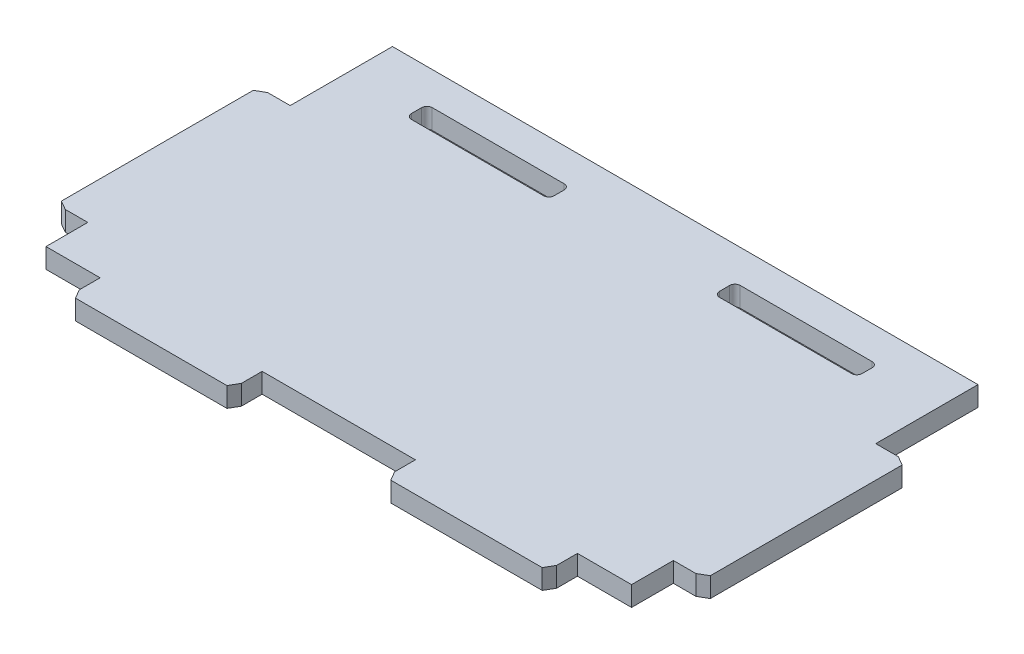
SolidWorks part; units mm, degrees
ref_plane "Front Plane" through (0, 0, 0) normal (0, 0, 1) x (1, 0, 0)
ref_plane "Top Plane" through (0, 0, 0) normal (0, 1, 0) x (1, 0, 0)
ref_plane "Right Plane" through (0, 0, 0) normal (1, 0, 0) x (0, 0, -1)
sketch "Sketch1" plane through (0, 0, 0) normal (0, 1, 0) x (1, 0, 0)
  line L1 (-46.8266, 25) -> (46.8266, 25)
  line L2 (-46.8266, 25) -> (-46.8266, -25)
  line L3 (-46.8266, -25) -> (46.8266, -25)
  line L4 (46.8266, 25) -> (46.8266, -25)
  line L5 (-46.8266, 25) -> (46.8266, -25) construction
  line L6 (-46.8266, -25) -> (46.8266, 25) construction
  point P0 (0, 0)
  dimension "D1" = 93.6531
  dimension "D2" = 50
extrude "Boss-Extrude1" add sketch "Sketch1" along normal blind 2.8575
sketch "Sketch3" plane through (0, 0, 0) normal (0, -1, 0) x (1, 0, 0)
  line L0 (-46.8266, 25) -> (46.8266, 25) construction
  line L2 (-34.1266, 25) -> (-34.1266, 29.318) construction
  line L5 (-34.1266, 29.318) -> (-11.3755, 29.318) construction
  line L6 (-11.3755, 29.318) -> (-11.3755, 25) construction
  line L7 (-11.3755, 25) -> (-34.1266, 25) construction
  line L8 (-11.3755, 27.159) -> (11.3755, 27.159) construction
  line L9 (11.3755, 29.318) -> (34.1266, 29.318) construction
  line L10 (11.3755, 29.318) -> (11.3755, 25) construction
  line L11 (11.3755, 25) -> (34.1266, 25) construction
  line L12 (34.1266, 29.318) -> (34.1266, 25) construction
  line L13 (-46.8266, -25) -> (-46.8266, 25) construction
  line L14 (34.1266, 27.159) -> (46.8266, 27.159) construction
  line L15 (46.8266, 27.159) -> (46.8266, 25) construction
  line L16 (-34.1266, 27.159) -> (-46.8266, 27.159) construction
  line L17 (-46.8266, 27.159) -> (-46.8266, 25) construction
  line L18 (-34.4441, 25) -> (-34.4441, 29.318)
  line L19 (-34.4441, 29.318) -> (-11.058, 29.318)
  line L20 (-11.058, 29.318) -> (-11.058, 25)
  line L21 (11.058, 25) -> (11.058, 29.318)
  line L22 (11.058, 29.318) -> (34.4441, 29.318)
  line L23 (34.4441, 29.318) -> (34.4441, 25)
  line L24 (-22.751, 29.318) -> (-22.751, 25) construction
  line L25 (22.751, 29.318) -> (22.751, 25) construction
  line L26 (-11.058, 25) -> (-34.4441, 25)
  line L27 (11.058, 25) -> (34.4441, 25)
  dimension "D1" = 4.318
  dimension "D2" = 12.7
  dimension "D3" = 0.3175
extrude "Boss-Extrude2" add sketch "Sketch3" against normal up to surface (2.8575 mm away) up to face at (0, 2.8575, 0)
sketch "Sketch4" plane through (0, 2.8575, 0) normal (0, 1, 0) x (1, 0, 0)
  line L6 (46.8266, 25) -> (42.2546, 25)
  line L7 (46.8266, 25) -> (46.8266, 10.2425)
  line L8 (46.8266, 10.2425) -> (42.2546, 10.2425)
  line L9 (42.2546, 25) -> (42.2546, 10.2425)
  line L10 (46.8266, -25) -> (42.2546, -25)
  line L11 (46.8266, -25) -> (46.8266, -18.9675)
  line L12 (46.8266, -18.9675) -> (42.2546, -18.9675)
  line L13 (42.2546, -25) -> (42.2546, -18.9675)
  line L14 (-46.8266, -18.65) -> (46.8266, -18.65) construction
  line L15 (46.8266, -25) -> (46.8266, 25) construction
  line L16 (-46.8266, 9.925) -> (46.8266, 9.925) construction
  line L17 (44.5406, -18.9675) -> (44.5406, -18.65) construction
  line L18 (44.5406, 10.2425) -> (44.5406, 9.925) construction
  line L19 (46.8266, 25) -> (-46.8266, 25) construction
  line L20 (-46.8266, 21.825) -> (46.8266, 21.825) construction
  line L21 (-46.8266, 21.825) -> (-46.8266, 17.253) construction
  line L22 (-46.8266, 17.253) -> (46.8266, 17.253) construction
  line L23 (46.8266, 21.825) -> (46.8266, 17.253) construction
  line L24 (-46.8266, -25) -> (-34.4441, -25) construction
  line L25 (-46.8266, 25) -> (-42.2546, 25)
  line L26 (-46.8266, 25) -> (-46.8266, 10.2425)
  line L27 (-46.8266, 10.2425) -> (-42.2546, 10.2425)
  line L28 (-42.2546, 25) -> (-42.2546, 10.2425)
  line L29 (-46.8266, -25) -> (-42.2546, -25)
  line L30 (-46.8266, -25) -> (-46.8266, -18.9675)
  line L31 (-46.8266, -18.9675) -> (-42.2546, -18.9675)
  line L32 (-42.2546, -25) -> (-42.2546, -18.9675)
  line L33 (-46.8266, 25) -> (-46.8266, -25) construction
  dimension "D1" = 28.575
  dimension "D2" = 6.35
  dimension "D3" = 0.3175
  dimension "D4" = 4.572
  dimension "D6" = 3.175
extrude "Cut-Extrude1" cut sketch "Sketch4" against normal up to next
sketch "Sketch5" plane through (0, 0, 0) normal (0, -1, 0) x (1, 0, 0)
  line L0 (0, -25) -> (0, 0) construction
  line L1 (12.7, -17.253) -> (31.75, -17.253) construction
  line L2 (12.7, -17.253) -> (12.7, -20.1105) construction
  line L3 (12.7, -20.1105) -> (31.75, -20.1105) construction
  line L4 (31.75, -17.253) -> (31.75, -20.1105) construction
  line L5 (42.2546, -25) -> (-42.2546, -25) construction
  line L6 (-31.75, -17.253) -> (-12.7, -17.253) construction
  line L7 (-46.8266, -17.253) -> (46.8266, -17.253) construction
  line L9 (11.938, -17.253) -> (32.512, -17.253)
  line L14 (32.512, -17.253) -> (32.512, -20.2375)
  line L15 (11.938, -20.2375) -> (32.512, -20.2375)
  line L16 (11.938, -17.253) -> (11.938, -20.2375)
  line L17 (-31.75, -17.253) -> (-31.75, -20.1105) construction
  line L18 (-31.75, -20.1105) -> (-12.7, -20.1105) construction
  line L19 (-12.7, -17.253) -> (-12.7, -20.1105) construction
  line L21 (-31.75, -18.6818) -> (-32.512, -18.6818) construction
  line L22 (-32.512, -17.253) -> (-11.938, -17.253)
  line L23 (-11.938, -17.253) -> (-11.938, -20.2375)
  line L24 (-32.512, -20.2375) -> (-11.938, -20.2375)
  line L25 (-32.512, -17.253) -> (-32.512, -20.2375)
  line L26 (-12.7, -18.6818) -> (-11.938, -18.6818) construction
  line L27 (12.7, -18.6818) -> (11.938, -18.6818) construction
  line L28 (31.75, -18.6818) -> (32.512, -18.6818) construction
  line L32 (-22.225, -17.253) -> (-22.225, -20.1105) construction
  line L33 (22.225, -17.253) -> (22.225, -20.1105) construction
  dimension "D1" = 2.8575
  dimension "D2" = 19.05
  dimension "D3" = 0.127
  dimension "D4" = 0.762
  dimension "D5" = 44.45
  dimension "D8" = 0.762
extrude "Cut-Extrude2" cut sketch "Sketch5" against normal up to next
sketch "Sketch6" plane through (0, 0, 0) normal (0, -1, 0) x (1, 0, 0)
  line L0 (-44.2866, 4.3625) -> (-46.8266, 4.3625) construction
  line L19 (-46.8266, -10.2425) -> (-46.8266, 18.9675) construction
  line L20 (44.2866, 4.3625) -> (46.8266, 4.3625) construction
  line L21 (46.8266, 18.9675) -> (46.8266, -10.2425) construction
  line L33 (-22.751, 26.778) -> (-22.751, 29.318) construction
  line L34 (-11.058, 29.318) -> (-34.4441, 29.318) construction
  line L35 (22.751, 26.778) -> (22.751, 29.318) construction
  line L36 (34.4441, 29.318) -> (11.058, 29.318) construction
  line L37 (-44.2866, 1.3145) -> (-44.2866, 3.3465) construction
  line L38 (-44.2866, 3.3465) -> (-44.2866, 5.3785) construction
  line L39 (-44.2866, 5.3785) -> (-44.2866, 7.4105) construction
  line L40 (-25.799, 26.778) -> (-23.767, 26.778) construction
  line L41 (-23.767, 26.778) -> (-21.735, 26.778) construction
  line L42 (-21.735, 26.778) -> (-19.703, 26.778) construction
  line L43 (19.703, 26.778) -> (21.735, 26.778) construction
  line L44 (21.735, 26.778) -> (23.767, 26.778) construction
  line L45 (23.767, 26.778) -> (25.799, 26.778) construction
  circle A0 centre (-25.799, 26.778) radius 0.635
  circle A1 centre (-23.767, 26.778) radius 0.635
  circle A2 centre (-21.735, 26.778) radius 0.635
  circle A3 centre (-19.703, 26.778) radius 0.635
  circle A4 centre (19.703, 26.778) radius 0.635
  circle A5 centre (21.735, 26.778) radius 0.635
  circle A6 centre (23.767, 26.778) radius 0.635
  circle A7 centre (25.799, 26.778) radius 0.635
  circle A9 centre (44.2866, 4.3625) radius 0.635
  circle A11 centre (-44.2866, 7.4105) radius 0.635
  circle A12 centre (-44.2866, 5.3785) radius 0.635
  circle A13 centre (-44.2866, 3.3465) radius 0.635
  circle A14 centre (-44.2866, 1.3145) radius 0.635
  dimension "D5" = 1.27
  dimension "D1" = 2.54
  dimension "D6" = 2.032
extrude "Cut-Extrude3" cut sketch "Sketch6" against normal blind 0.127
chamfer "Chamfer1" distance 0.762 angle 60 4 edges at (46.8266, 1.4287, -10.2425) (-34.4441, 1.4287, 29.318) (11.058, 1.4287, 29.318) (-46.8266, 1.4287, 18.9675)
chamfer "Chamfer2" distance 0.762 angle 60 4 edges at (46.8266, 1.4287, 18.9675) (34.4441, 1.4287, 29.318) (-11.058, 1.4287, 29.318) (-46.8266, 1.4287, -10.2425)
fillet "Fillet1" radius 0.762 8 edges at (11.938, 1.4287, -20.2375) (11.938, 1.4287, -17.253) (32.512, 1.4287, -17.253) (32.512, 1.4287, -20.2375) (-32.512, 1.4287, -17.253) (-32.512, 1.4287, -20.2375) (-11.938, 1.4287, -20.2375) (-11.938, 1.4287, -17.253)
